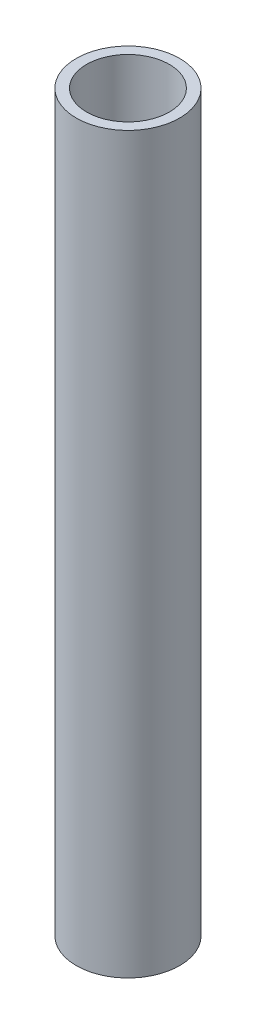
SolidWorks part; units mm, degrees
ref_plane "Alzado" through (0, 0, 0) normal (0, 0, 1) x (1, 0, 0)
ref_plane "Planta" through (0, 0, 0) normal (0, 1, 0) x (1, 0, 0)
ref_plane "Vista lateral" through (0, 0, 0) normal (1, 0, 0) x (0, 0, -1)
sketch "Croquis1" plane through (0, 0, 0) normal (0, 1, 0) x (1, 0, 0)
  circle A0 centre (0, 0) radius 5
  circle A1 centre (0, 0) radius 4
  dimension "D1" = 10
  dimension "D2" = 1
extrude "Saliente-Extruir1" add sketch "Croquis1" along normal blind 71
